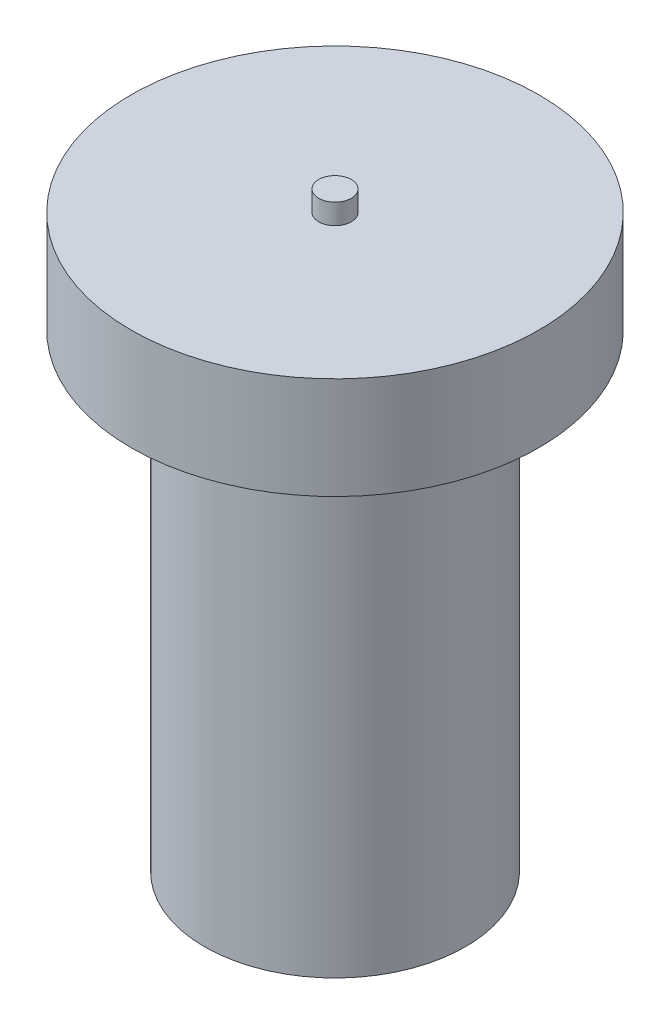
SolidWorks part; units mm, degrees
ref_plane "Front Plane" through (0, 0, 0) normal (0, 0, 1) x (1, 0, 0)
ref_plane "Top Plane" through (0, 0, 0) normal (0, 1, 0) x (1, 0, 0)
ref_plane "Right Plane" through (0, 0, 0) normal (1, 0, 0) x (0, 0, -1)
sketch "Sketch1" plane through (0, 0, 0) normal (0, 1, 0) x (1, 0, 0)
  circle A0 centre (0, 0) radius 32
  dimension "D1" = 64
extrude "Boss-Extrude1" add sketch "Sketch1" along normal blind 110
sketch "Sketch2" plane through (0, 110, 0) normal (0, 1, 0) x (1, 0, 0)
  circle A0 centre (0, 0) radius 5
extrude "Boss-Extrude2" add sketch "Sketch2" along normal blind 5
sketch "Sketch3" plane through (0, 115, 0) normal (0, 1, 0) x (1, 0, 0)
  circle A0 centre (0, 0) radius 50
  dimension "D1" = 100
extrude "Boss-Extrude3" add sketch "Sketch3" along normal blind 25
sketch "Sketch4" plane through (0, 140, 0) normal (0, 1, 0) x (1, 0, 0)
  circle A0 centre (0, 0) radius 4
  dimension "D1" = 8
extrude "Boss-Extrude4" add sketch "Sketch4" along normal blind 5
sketch "Sketch5" plane through (0, 0, 0) normal (0, -1, 0) x (1, 0, 0)
  circle A0 centre (0, 0) radius 15
  dimension "D1" = 30
extrude "Boss-Extrude5" add sketch "Sketch5" along normal blind 4
